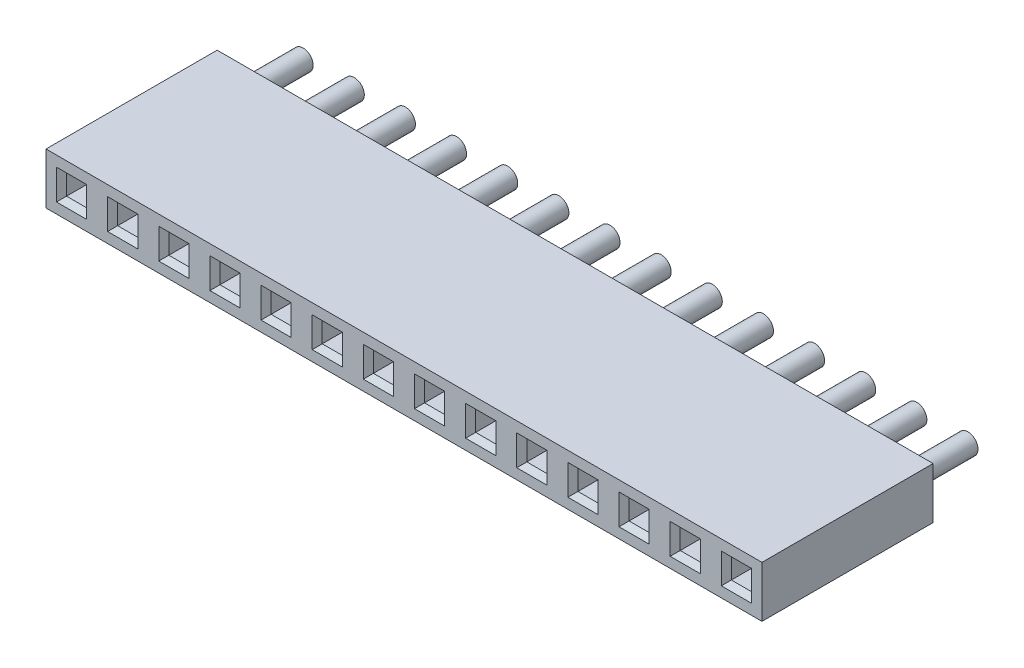
SolidWorks part; units mm, degrees
ref_plane "Front Plane" through (0, 0, 0) normal (0, 0, 1) x (1, 0, 0)
ref_plane "Top Plane" through (0, 0, 0) normal (0, 1, 0) x (1, 0, 0)
ref_plane "Right Plane" through (0, 0, 0) normal (1, 0, 0) x (0, 0, -1)
sketch "Sketch1" plane through (0, 0, 0) normal (0, 0, 1) x (1, 0, 0)
  line L1 (0, 0) -> (35.56, 0)
  line L2 (0, 0) -> (0, 2.54)
  line L3 (0, 2.54) -> (35.56, 2.54)
  line L4 (35.56, 0) -> (35.56, 2.54)
  dimension "D1" = 2.54
  dimension "D2" = 35.56
extrude "Boss-Extrude1" add sketch "Sketch1" along normal blind 8.5
sketch "Sketch2" plane through (0, 0, 8.5) normal (0, 0, 1) x (1, 0, 0)
  line L0 (0, 0) -> (35.56, 0) construction
  line L1 (0.77, 0.77) -> (1.77, 0.77)
  line L2 (0.77, 0.77) -> (0.77, 1.77)
  line L3 (0.77, 1.77) -> (1.77, 1.77)
  line L4 (1.77, 0.77) -> (1.77, 1.77)
  line L5 (0, 2.54) -> (0, 0) construction
  dimension "D1" = 1
  dimension "D2" = 1
  dimension "D3" = 0.77
  dimension "D4" = 0.77
extrude "Cut-Extrude1" cut sketch "Sketch2" against normal blind 8
chamfer "Chamfer1" distance 0.25 angle 45 4 edges at (1.27, 0.77, 8.5) (1.77, 1.27, 8.5) (0.77, 1.27, 8.5) (1.27, 1.77, 8.5)
pattern_linear "LPattern2" count 14 spacing 2.54 along (1, 0, 0) of "Chamfer1", "Cut-Extrude1"
sketch "Sketch3" plane through (0, 0, 0) normal (0, 0, -1) x (-1, 0, 0)
  line L0 (0, 0) -> (-35.56, 0) construction
  line L1 (0, 2.54) -> (0, 0) construction
  circle A0 centre (-1.27, 1.27) radius 0.5
  dimension "D1" = 1
  dimension "D2" = 1.27
  dimension "D3" = 1.27
extrude "Boss-Extrude2" add sketch "Sketch3" along normal blind 3
pattern_linear "LPattern3" count 14 spacing 2.54 along (1, 0, 0) of "Boss-Extrude2"
